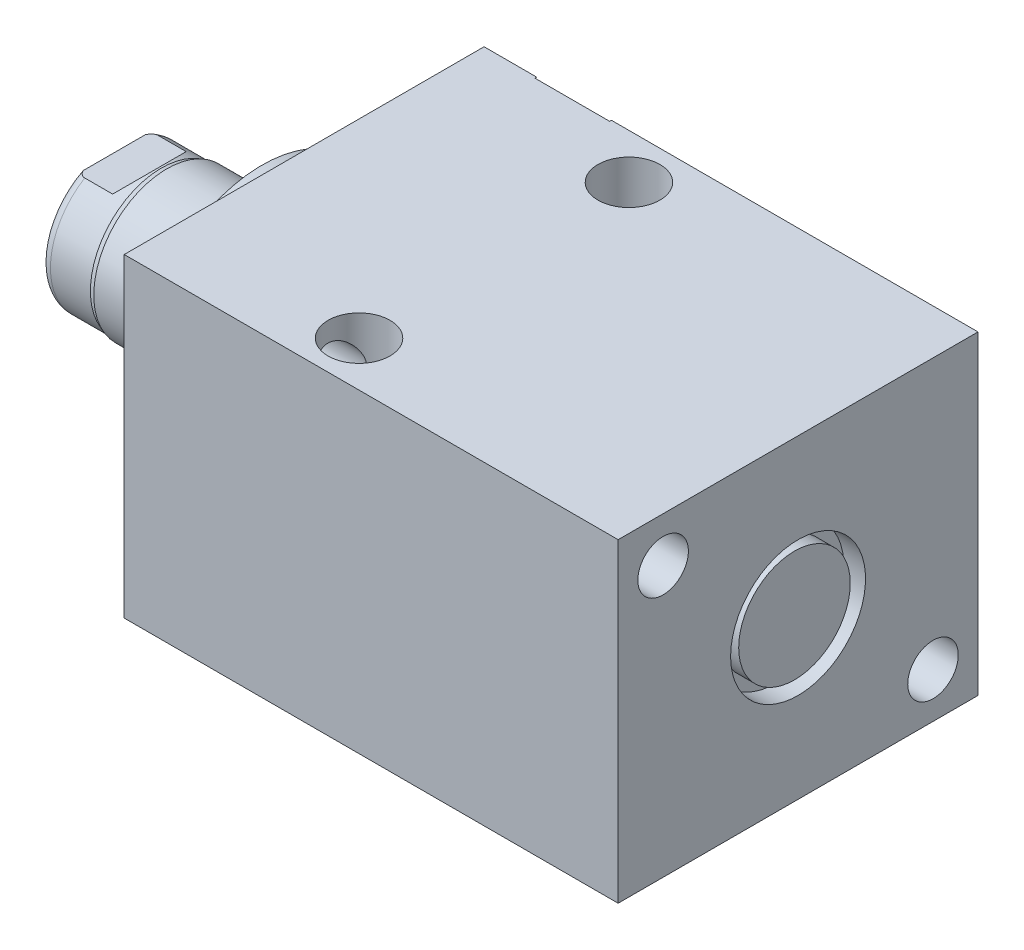
SolidWorks part; units mm, degrees
material "Alloy Steel"
ref_plane "Front Plane" through (0, 0, 0) normal (0, 0, 1) x (1, 0, 0)
ref_plane "Top Plane" through (0, 0, 0) normal (0, 1, 0) x (1, 0, 0)
ref_plane "Right Plane" through (0, 0, 0) normal (1, 0, 0) x (0, 0, -1)
ref_plane "Plane1" through (0, 0, 0) normal (1, 0, 0) x (0, 0, -1)
sketch "Sketch1" plane through (0, 0, 0) normal (1, 0, 0) x (0, 0, -1)
  line L0 (-25.4, 22.225) -> (25.4, 22.225)
  line L1 (25.4, 22.225) -> (25.4, -22.225)
  line L2 (25.4, -22.225) -> (-25.4, -22.225)
  line L3 (-25.4, -22.225) -> (-25.4, 22.225)
  line L4 (0, -24.4475) -> (0, 24.4475) construction
  dimension "D1" = 44.45
  dimension "D2" = 22.225
  dimension "D3" = 50.8
extrude "Extrude1" add sketch "Sketch1" along normal blind 69.723
ref_plane "Plane12" through (0, 14.3002, 0) normal (0, 1, 0) x (-1, 0, 0)
sketch "S2D0002" plane through (0, 14.3002, 0) normal (0, 1, 0) x (-1, 0, 0)
  line L0 (-18.8849, -25.146) -> (-22.225, -25.146)
  line L1 (-18.8849, -25.146) -> (-18.3423, -22.5933)
  line L2 (-18.3423, -22.5933) -> (-17.6784, -21.9294)
  line L3 (-17.6784, -21.9294) -> (-17.6784, -11.176)
  line L4 (-17.6784, -11.176) -> (-12.7, -11.176)
  line L5 (-12.7, -11.176) -> (-12.7, -25.4)
  line L6 (-12.7, -19.1384) -> (-12.7, 0.6985) construction
  line L7 (0, -25.4) -> (0, 25.4) construction
  line L8 (-22.225, -25.4) -> (-22.225, -25.146)
  line L9 (-69.723, -25.4) -> (0, -25.4) construction
  line L10 (-22.225, -25.4) -> (-12.7, -25.4)
  dimension "D1" = 14.224
  dimension "D2" = 12.7
  dimension "D3" = 9.9568
  dimension "D4" = 45
  dimension "D5" = 12.3698
  dimension "D6" = 12
  dimension "D7" = 2.5527
  dimension "D8" = 0.254
  dimension "D9" = 19.05
revolve "Cut-Revolve1" cut sketch "S2D0002" angle 360 about L6
ref_plane "Plane3" through (41.148, 0, -25.146) normal (0, 1, 0) x (1, 0, 0)
sketch "Sketch3" plane through (41.148, 0, -25.146) normal (0, 1, 0) x (1, 0, 0)
  line L0 (18.8849, 0) -> (22.225, 0)
  line L1 (18.8849, 0) -> (18.3423, -2.5527)
  line L2 (18.3423, -2.5527) -> (17.6784, -3.2166)
  line L3 (17.6784, -3.2166) -> (17.6784, -13.97)
  line L4 (17.6784, -13.97) -> (12.7, -13.97)
  line L5 (12.7, -13.97) -> (12.7, 0.254)
  line L6 (12.7, -21.9564) -> (12.7, 0.6985) construction
  line L7 (-41.148, 0.254) -> (-41.148, -50.546) construction
  line L8 (22.225, 0.254) -> (22.225, 0)
  line L9 (28.575, 0.254) -> (-23.1638, 0.254) construction
  line L10 (22.225, 0.254) -> (12.7, 0.254)
  dimension "D1" = 14.224
  dimension "D2" = 53.848
  dimension "D3" = 9.9568
  dimension "D4" = 45
  dimension "D5" = 12
  dimension "D6" = 12.3698
  dimension "D7" = 2.5527
  dimension "D8" = 0.254
  dimension "D9" = 19.05
revolve "Cut-Revolve2" cut sketch "Sketch3" angle 360 about L6
ref_plane "Plane4" through (53.975, 0, 0) normal (0, 0, 1) x (0, -1, 0)
sketch "Sketch4" plane through (53.975, 0, 0) normal (0, 0, 1) x (0, -1, 0)
  line L0 (6.1849, 12.7) -> (9.525, 12.7)
  line L1 (6.1849, 12.7) -> (5.6423, 10.1473)
  line L2 (5.6423, 10.1473) -> (4.9784, 9.4834)
  line L3 (4.9784, 9.4834) -> (4.9784, 1.3462)
  line L4 (4.9784, 1.3462) -> (0, 1.3462)
  line L5 (0, 1.3462) -> (0, 15.748)
  line L6 (0, -15.0954) -> (0, 0.5677) construction
  line L7 (0, 15.748) -> (9.525, 15.748)
  line L9 (-22.225, 15.748) -> (22.225, 15.748) construction
  line L10 (9.525, 15.748) -> (9.525, 12.7)
  dimension "D1" = 11.3538
  dimension "D2" = 9.9568
  dimension "D3" = 3.048
  dimension "D4" = 19.05
  dimension "D5" = 2.5527
  dimension "D6" = 12
  dimension "D7" = 45
  dimension "D8" = 12.3698
revolve "Cut-Revolve3" cut sketch "Sketch4" angle 360 about L6
sketch "Sketch5" plane through (0, 0, 0) normal (-1, 0, 0) x (0, 0, 1)
  circle A0 centre (0, 0) radius 17.4625
  dimension "D1" = 34.925
extrude "Extrude2" add sketch "Sketch5" along normal blind 5.969
ref_plane "Plane5" through (0, 0, 0) normal (0, -1, 0) x (0, 0, 1)
sketch "Sketch6" plane through (0, 0, 0) normal (0, -1, 0) x (0, 0, 1)
  line L0 (0, 5.969) -> (-10.3187, 5.969)
  line L1 (-10.3187, 5.969) -> (-10.3187, 26.797)
  line L2 (-10.3187, 26.797) -> (0, 26.797)
  line L3 (0, 26.797) -> (0, 5.969)
  line L4 (0, -5.7546) -> (0, 21.1709) construction
  line L5 (17.4625, 5.969) -> (-17.4625, 5.969) construction
  line L6 (25.4, -69.723) -> (-25.4, -69.723) construction
  dimension "D1" = 96.52
  dimension "D2" = 20.6375
revolve "Revolve1" add sketch "Sketch6" angle 360 about L4
ref_plane "Plane6" through (-18.5113, 3.2639, 0) normal (0, 0, 1) x (0, 1, 0)
sketch "S2D0001" plane through (-18.5113, 3.2639, 0) normal (0, 0, 1) x (0, 1, 0)
  line L0 (0, 6.35) -> (0, -6.5225)
  line L1 (0, -6.5225) -> (-3.2639, -6.5225)
  line L2 (1.1176, 8.2857) -> (-3.2639, 8.2857)
  line L3 (-3.2639, 8.2857) -> (-3.2639, -6.5225)
  line L4 (0, 6.35) -> (1.1176, 8.2857)
  line L5 (-3.2639, -18.5113) -> (-3.2639, 2.765) construction
  line L6 (7.0549, 8.2857) -> (-13.5826, 8.2857) construction
  dimension "D1" = 30
  dimension "D2" = 8.763
  dimension "D3" = 6.5278
  dimension "D4" = 14.8082
revolve "Cut-Revolve4" cut sketch "S2D0001" angle 360 about L5
ref_plane "Plane7" through (0, 0, 0) normal (0, 1, 0) x (0, 0, -1)
sketch "Sketch8" plane through (0, 0, 0) normal (0, 1, 0) x (0, 0, -1)
  line L0 (-10.3187, 19.3802) -> (-10.033, 20.1422)
  line L1 (-10.033, 20.1422) -> (-10.033, 25.781)
  line L2 (0, 12.6594) -> (0, 20.8178) construction
  line L3 (-10.3187, 19.3802) -> (-10.3187, 26.797)
  line L4 (-9.6449, 26.797) -> (-10.3187, 26.797)
  line L5 (10.3187, 26.797) -> (-10.3187, 26.797) construction
  line L6 (-10.3187, 26.797) -> (-10.3187, 5.969) construction
  arc A0 (-9.6449, 26.797) -> (-10.033, 25.781) centre (-8.509, 25.781) ccw
  dimension "D2" = 1.524
  dimension "D1" = 20.066
  dimension "D3" = 1.016
  dimension "D4" = 0.762
  dimension "D5" = 6.6548
revolve "Cut-Revolve5" cut sketch "Sketch8" angle 360 about L2
ref_plane "Plane11" through (0, 0, 0) normal (0, 0, -1) x (0, -1, 0)
sketch "Sketch12" plane through (0, 0, 0) normal (0, 0, -1) x (0, -1, 0)
  line L0 (8.5852, 26.797) -> (8.5852, 21.844)
  line L1 (8.5852, 21.844) -> (10.033, 20.3962)
  line L2 (-8.5852, 26.797) -> (-8.5852, 21.844)
  line L3 (-8.5852, 21.844) -> (-10.033, 20.3962)
  line L4 (8.5852, 26.797) -> (10.033, 26.797)
  line L5 (0, 13.7262) -> (0, 20.767) construction
  line L6 (-10.033, 20.3962) -> (-10.033, 26.797)
  line L7 (9.6449, 26.797) -> (-9.6449, 26.797) construction
  line L8 (10.033, 20.1422) -> (10.033, 25.781) construction
  line L9 (10.033, 20.3962) -> (10.033, 26.797)
  line L10 (-8.5852, 26.797) -> (-10.033, 26.797)
  dimension "D1" = 17.1704
  dimension "D2" = 4.953
  dimension "D3" = 45
extrude "Cut-Extrude4" cut sketch "Sketch12" against normal mid plane 60.96
sketch "Sketch13" plane through (0, 0, -25.146) normal (0, 0, -1) x (-1, 0, 0)
  circle A0 centre (-53.848, 0) radius 7.874
  circle A2 centre (-53.848, 0) radius 6.1849 construction
  dimension "D1" = 15.748
extrude "Extrude3" add sketch "Sketch13" along normal blind 2.54
hole_wizard "Hole1" positions "Sketch15" profile "Sketch14" legacy end condition up to next
sketch "Sketch15" plane through (0, 0, 0) normal (-1, 0, 0) x (0, 0, 1)
  line L0 (0, 0) -> (-29.9914, 0) construction
  line L1 (0, 0) -> (0, 25.7648) construction
  point P0 (-19.05, -15.875)
  point P11 (19.05, 15.875)
  dimension "D1" = 15.875
  dimension "D2" = 19.05
  dimension "D3" = 31.75
  dimension "D4" = 38.1
sketch "Sketch14" plane through (0, -15.875, -19.05) normal (0, 1, 0) x (0, 0, 1)
  line L0 (0, 0) -> (0, 69.723)
  line L1 (0, 69.723) -> (3.5687, 69.723)
  line L2 (3.5687, 69.723) -> (3.5687, 0)
  line L3 (3.5687, 0) -> (0, 0)
  line L4 (0, 110) -> (0, -10) construction
  dimension "Diameter" = 7.1374
  dimension "Depth" = 69.723
hole_wizard "Hole2" positions "Sketch17" profile "Sketch16" legacy
sketch "Sketch17" plane through (0, 22.225, 0) normal (0, 1, 0) x (-1, 0, 0)
  line L0 (0, 0) -> (-59.3363, 0) construction
  line L1 (0, -25.4) -> (0, 25.4) construction
  point P0 (-26.797, -19.05)
  point P9 (-26.797, 19.05)
  dimension "D1" = 38.1
  dimension "D2" = 26.797
sketch "Sketch16" plane through (26.797, 22.225, -19.05) normal (1, 0, 0) x (0, 0, 1)
  line L0 (0, 0) -> (0, 44.45)
  line L1 (0, 44.45) -> (4.3688, 44.45)
  line L2 (4.3688, 44.45) -> (4.3688, 0)
  line L3 (4.3688, 0) -> (0, 0)
  line L4 (0, 110) -> (0, -10) construction
  dimension "Diameter" = 8.7376
  dimension "Depth" = 44.45
sketch "Sketch18" plane through (66.675, 0, 0) normal (1, 0, 0) x (0, 0, -1)
  circle A0 centre (0, 0) radius 7.874
  dimension "D1" = 15.748
extrude "Extrude4" add sketch "Sketch18" along normal blind 2.54
